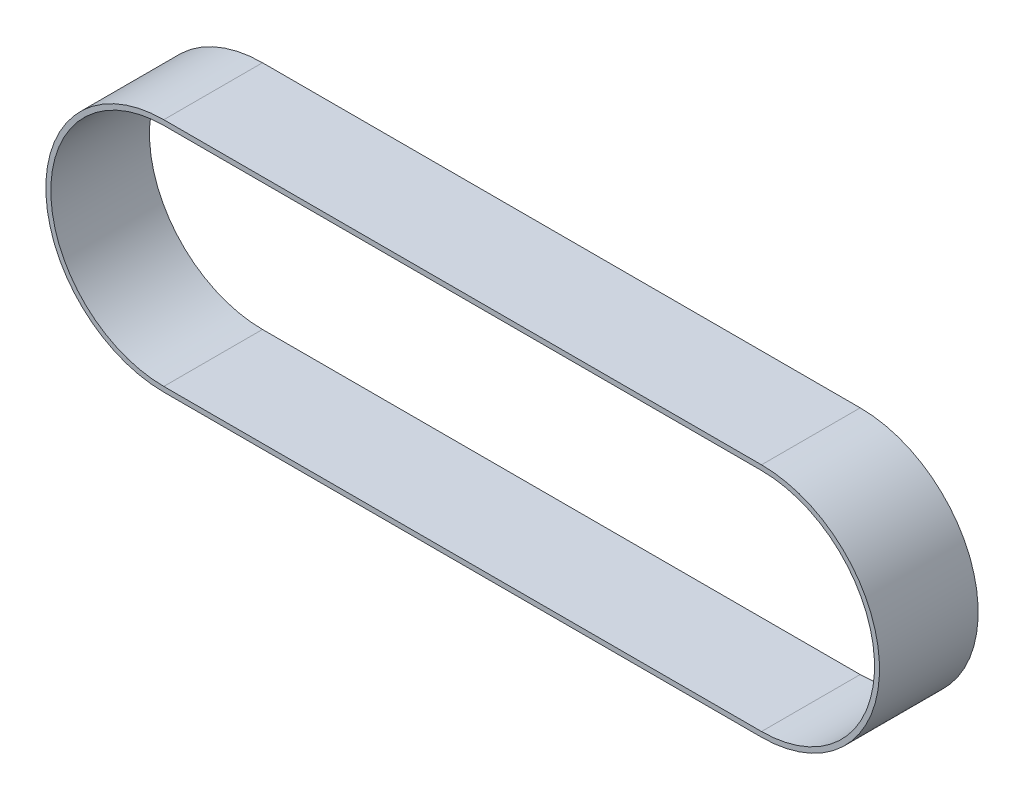
SolidWorks part; units mm, degrees
ref_plane "Front Plane" through (0, 0, 0) normal (0, 0, 1) x (1, 0, 0)
ref_plane "Top Plane" through (0, 0, 0) normal (0, 1, 0) x (1, 0, 0)
ref_plane "Right Plane" through (0, 0, 0) normal (1, 0, 0) x (0, 0, -1)
sketch "Sketch1" plane through (0, 0, 0) normal (0, 0, 1) x (1, 0, 0)
  line L0 (16.002, 22.6886) -> (24.003, 22.6886) construction
  line L1 (0, 45.3771) -> (120.015, 45.3771)
  line L2 (0, 45.3771) -> (0, 0) construction
  line L3 (0, 0) -> (120.015, 0)
  line L4 (24.003, 22.6886) -> (32.004, 22.6886) construction
  line L5 (0, 22.6886) -> (8.001, 22.6886) construction
  line L6 (8.001, 22.6886) -> (16.002, 22.6886) construction
  line L7 (32.004, 22.6886) -> (40.005, 22.6886) construction
  line L8 (40.005, 22.6886) -> (48.006, 22.6886) construction
  line L9 (48.006, 22.6886) -> (56.007, 22.6886) construction
  line L10 (56.007, 22.6886) -> (64.008, 22.6886) construction
  line L11 (64.008, 22.6886) -> (72.009, 22.6886) construction
  line L12 (72.009, 22.6886) -> (80.01, 22.6886) construction
  line L13 (80.01, 22.6886) -> (88.011, 22.6886) construction
  line L14 (88.011, 22.6886) -> (96.012, 22.6886) construction
  line L15 (96.012, 22.6886) -> (104.013, 22.6886) construction
  line L16 (104.013, 22.6886) -> (112.014, 22.6886) construction
  line L17 (120.015, 45.3771) -> (120.015, 0) construction
  line L18 (112.014, 22.6886) -> (120.015, 22.6886) construction
  line L21 (0, 46.3771) -> (120.015, 46.3771)
  line L22 (0, -1) -> (120.015, -1)
  arc A0 (120.015, 45.3771) -> (120.015, 0) centre (120.015, 22.6885) cw
  arc A1 (0, 45.3771) -> (0, 0) centre (0, 22.6886) ccw
  arc A7 (120.015, 46.3771) -> (120.015, -1) centre (120.015, 22.6886) cw
  arc A8 (0, 46.3771) -> (0, -1) centre (0, 22.6886) ccw
  dimension "D1" = 8.001
  dimension "D4" = 1
  dimension "D3" = 45.3771
extrude "Boss-Extrude1" add sketch "Sketch1" along normal mid plane 19.812
